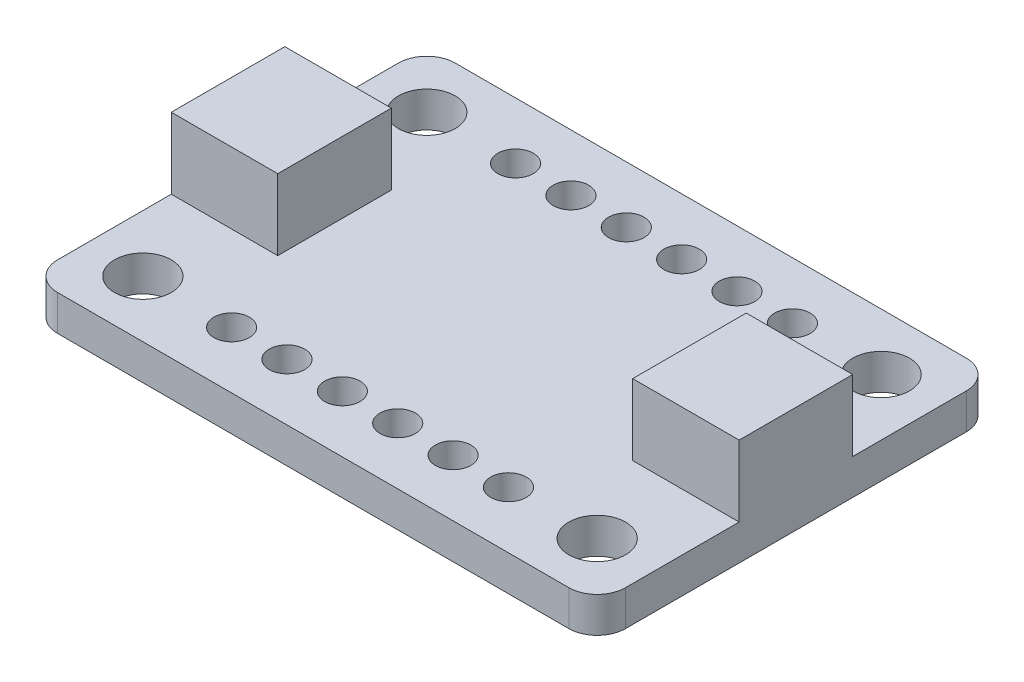
SolidWorks part; units mm, degrees
ref_plane "Front Plane" through (0, 0, 0) normal (0, 0, 1) x (1, 0, 0)
ref_plane "Top Plane" through (0, 0, 0) normal (0, 1, 0) x (1, 0, 0)
ref_plane "Right Plane" through (0, 0, 0) normal (1, 0, 0) x (0, 0, -1)
sketch "Sketch1" plane through (0, 0, 0) normal (0, 1, 0) x (1, 0, 0)
  line L1 (1.27, 0) -> (24.13, 0)
  line L2 (0, 1.27) -> (0, 16.51)
  line L3 (1.27, 17.78) -> (24.13, 17.78)
  line L4 (25.4, 1.27) -> (25.4, 16.51)
  circle A0 centre (2.54, 15.24) radius 1.27
  circle A1 centre (22.86, 15.24) radius 1.27
  circle A2 centre (22.86, 2.54) radius 1.27
  circle A3 centre (2.54, 2.54) radius 1.27
  arc A4 (0, 16.51) -> (1.27, 17.78) centre (1.27, 16.51) cw
  arc A5 (25.4, 16.51) -> (24.13, 17.78) centre (24.13, 16.51) ccw
  arc A6 (24.13, 0) -> (25.4, 1.27) centre (24.13, 1.27) ccw
  arc A7 (0, 1.27) -> (1.27, 0) centre (1.27, 1.27) ccw
  point P21 (0, 0)
  dimension "D3" = 2.54
  dimension "D1" = 25.4
  dimension "D2" = 17.78
  dimension "D4" = 20.32
  dimension "D5" = 2.54
  dimension "D6" = 2.54
  dimension "D7" = 2.54
extrude "Boss-Extrude1" add sketch "Sketch1" along normal blind 1.5875
sketch "Sketch2" plane through (0, 1.5875, 0) normal (0, 1, 0) x (1, 0, 0)
  line L0 (0, 16.51) -> (0, 1.27) construction
  line L1 (0, 6.35) -> (4.7625, 6.35)
  line L2 (0, 6.35) -> (0, 11.43)
  line L3 (0, 11.43) -> (4.7625, 11.43)
  line L4 (4.7625, 6.35) -> (4.7625, 11.43)
  line L5 (1.27, 0) -> (24.13, 0) construction
  line L6 (24.13, 17.78) -> (1.27, 17.78) construction
  line L7 (25.4, 1.27) -> (25.4, 16.51) construction
  line L8 (25.4, 6.35) -> (20.6375, 6.35)
  line L9 (25.4, 6.35) -> (25.4, 11.43)
  line L10 (25.4, 11.43) -> (20.6375, 11.43)
  line L11 (20.6375, 6.35) -> (20.6375, 11.43)
  circle A0 centre (2.54, 15.24) radius 1.9844
  circle A1 centre (22.86, 15.24) radius 1.9844
  circle A2 centre (22.86, 2.54) radius 1.9844
  circle A3 centre (2.54, 2.54) radius 1.9844
  circle A4 centre (6.5087, 15.24) radius 0.7938
  circle A5 centre (8.9852, 15.24) radius 0.7937
  circle A6 centre (11.4617, 15.24) radius 0.7937
  circle A7 centre (13.9382, 15.24) radius 0.7937
  circle A9 centre (16.4147, 15.24) radius 0.7937
  circle A10 centre (18.8912, 15.24) radius 0.7937
  circle A11 centre (6.5087, 2.54) radius 0.7938
  circle A12 centre (8.9852, 2.54) radius 0.7937
  circle A13 centre (11.4617, 2.54) radius 0.7937
  circle A14 centre (13.9382, 2.54) radius 0.7937
  circle A15 centre (16.4147, 2.54) radius 0.7937
  circle A16 centre (18.8912, 2.54) radius 0.7937
  dimension "D7" = 3.9688
  dimension "D8" = 3.9688
  dimension "D15" = 1.5875
  dimension "D1" = 6.35
  dimension "D2" = 6.35
  dimension "D3" = 4.7625
  dimension "D4" = 4.7625
  dimension "D5" = 6.35
  dimension "D6" = 6.35
  dimension "D9" = 3.9688
  dimension "D10" = 2.4765
  dimension "D11" = 2.4765
  dimension "D12" = 2.4765
  dimension "D13" = 2.4765
  dimension "D14" = 2.4765
extrude "Cut-Extrude1" cut sketch "Sketch2" against normal blind 1.5875 contours A11 | A12 | A13 | A14 | A15 | A16 | A9 | A7 | A6 | A5 | A4 | A10
sketch "Sketch4" plane through (0, 1.5875, 0) normal (0, 1, 0) x (1, 0, 0)
  line L0 (25.4, 1.27) -> (25.4, 16.51) construction
  line L1 (25.4, 6.35) -> (20.6375, 6.35)
  line L2 (25.4, 6.35) -> (25.4, 11.43)
  line L3 (25.4, 11.43) -> (20.6375, 11.43)
  line L4 (20.6375, 6.35) -> (20.6375, 11.43)
  line L5 (24.13, 17.78) -> (1.27, 17.78) construction
  line L6 (1.27, 0) -> (24.13, 0) construction
  line L7 (0, 16.51) -> (0, 1.27) construction
  line L8 (0, 6.35) -> (4.7625, 6.35)
  line L9 (0, 6.35) -> (0, 11.43)
  line L10 (0, 11.43) -> (4.7625, 11.43)
  line L11 (4.7625, 6.35) -> (4.7625, 11.43)
  dimension "D1" = 6.35
  dimension "D2" = 6.35
  dimension "D3" = 4.7625
  dimension "D4" = 6.35
  dimension "D5" = 6.35
  dimension "D6" = 4.7625
extrude "Boss-Extrude2" add sketch "Sketch4" along normal blind 3.175
